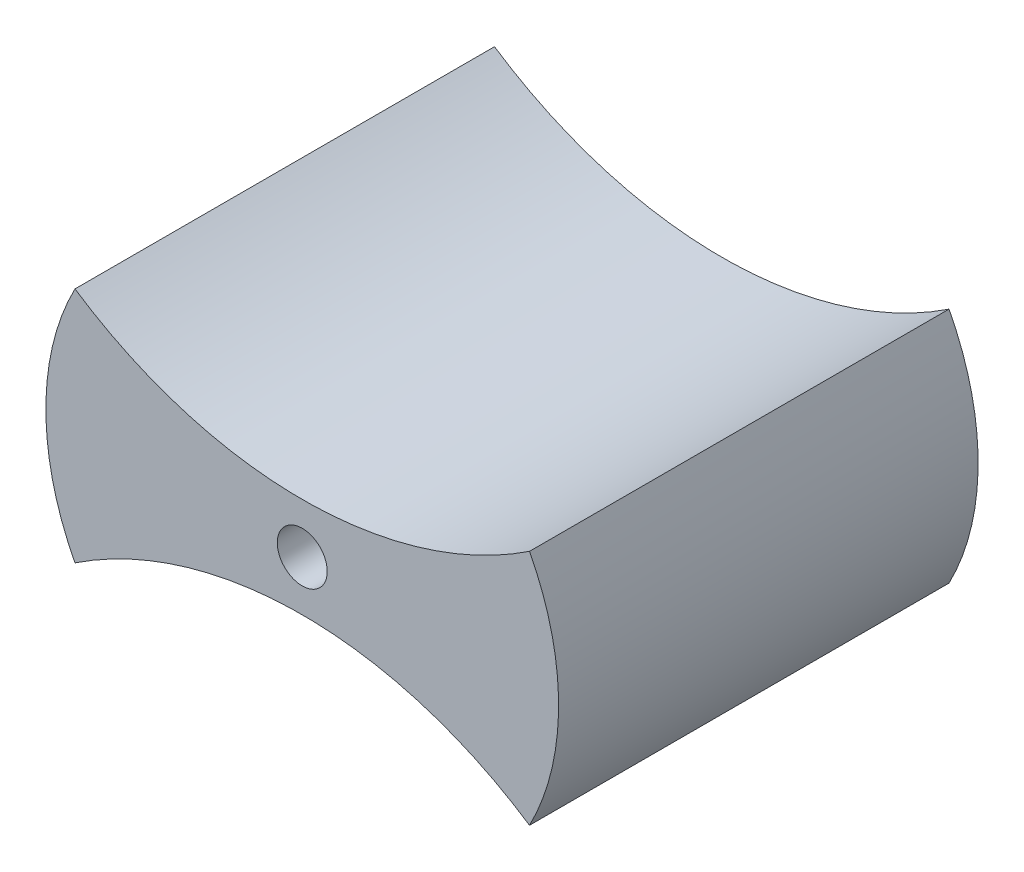
SolidWorks part; units mm, degrees
ref_plane "前视基准面" through (0, 0, 0) normal (0, 0, 1) x (1, 0, 0)
ref_plane "上视基准面" through (0, 0, 0) normal (0, 1, 0) x (1, 0, 0)
ref_plane "右视基准面" through (0, 0, 0) normal (1, 0, 0) x (0, 0, -1)
sketch "草图1" plane through (0, 0, 0) normal (0, 0, 1) x (1, 0, 0)
  line L1 (-15.4, 3) -> (15.4, 3)
  line L2 (-15.4, 3) -> (-15.4, 0)
  line L3 (-15.105, -3) -> (15.4, -3)
  line L4 (15.4, 3) -> (15.4, -3)
  line L5 (0, -3) -> (0, 3) construction
  line L6 (-15.4, 0) -> (15.4, 0) construction
  arc A0 (-13.6518, 7.1265) -> (-13.6518, -7.1265) centre (0, 0) ccw
  arc A1 (13.6518, 7.1265) -> (13.6518, -7.1265) centre (0, 0) cw
  arc A2 (-13.6518, 7.1265) -> (13.6518, 7.1265) centre (0, 27.6456) ccw
  arc A3 (-13.6518, -7.1265) -> (13.6518, -7.1265) centre (0, -27.6456) cw
  circle A4 centre (0, 0) radius 1.5
  point P0 (0, 0)
  dimension "D1" = 3
  dimension "D2" = 30.8
extrude "凸台-拉伸1" add sketch "草图1" along normal blind 25.2 contours A2 A0 L1 | A1 L1 A0 L3 A4 | A0 A3 L3 | A2 L1 A1 | L3 A3 A1
